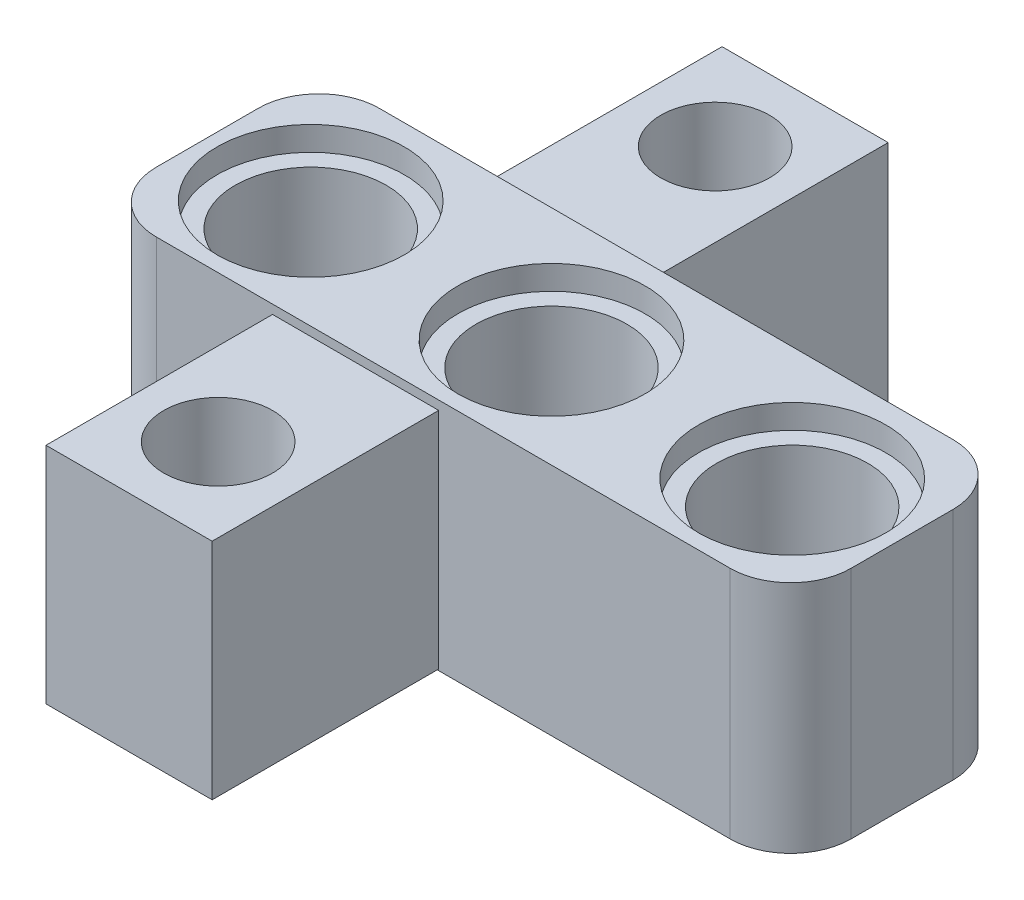
SolidWorks part; units mm, degrees
ref_plane "Front Plane" through (0, 0, 0) normal (0, 0, 1) x (1, 0, 0)
ref_plane "Top Plane" through (0, 0, 0) normal (0, 1, 0) x (1, 0, 0)
ref_plane "Right Plane" through (0, 0, 0) normal (1, 0, 0) x (0, 0, -1)
sketch "Sketch3" plane through (0, 0, 0) normal (0, 1, 0) x (1, 0, 0)
  line L1 (0, 0) -> (-23, 0)
  line L2 (0, 0) -> (0, 7.38)
  line L3 (0, 7.38) -> (-23, 7.38)
  line L4 (-23, 0) -> (-23, 7.38)
  dimension "D1" = 23
  dimension "D2" = 7.38
extrude "Boss-Extrude1" add sketch "Sketch3" along normal blind 7.76
sketch "Sketch4" plane through (0, 0, 0) normal (0, -1, 0) x (-1, 0, 0)
  line L0 (23, 0) -> (0, 0) construction
  circle A0 centre (19.5383, 3.69) radius 3.1
  circle A1 centre (11.5383, 3.69) radius 3.1
  circle A2 centre (3.5383, 3.69) radius 3.1
  dimension "D1" = 6.2
  dimension "D2" = 3.69
  dimension "D3" = 3
extrude "Cut-Extrude2" cut sketch "Sketch4" against normal blind 0.8
sketch "Sketch6" plane through (0, 0.8, 0) normal (0, -1, 0) x (-1, 0, 0)
  circle A0 centre (3.5383, 3.5915) radius 2.5
  circle A1 centre (3.5383, 3.69) radius 3.1 construction
  circle A2 centre (11.5083, 3.5915) radius 2.5
  circle A3 centre (19.4783, 3.5915) radius 2.5
  dimension "D2" = 5
  dimension "D1" = 0
  dimension "D3" = 3
sketch "Sketch7" plane through (0, 7.76, 0) normal (0, 1, 0) x (1, 0, 0)
  circle A0 centre (-19.4783, 3.5915) radius 3.1
  circle A3 centre (-11.5083, 3.5915) radius 3.1
  circle A4 centre (-3.5383, 3.5915) radius 3.1
  dimension "D1" = 6.2
  dimension "D2" = 3
extrude "Cut-Extrude3" cut sketch "Sketch7" against normal blind 0.8
extrude "Cut-Extrude4" cut sketch "Sketch6" against normal through all
fillet "Fillet3" radius 2 1 edges at (0, 3.88, 0)
fillet "Fillet4" radius 2 1 edges at (-23, 3.88, 0)
fillet "Fillet5" radius 2 1 edges at (-23, 3.88, -7.38)
fillet "Fillet6" radius 2 1 edges at (0, 3.88, -7.38)
sketch "Sketch8" plane through (0, 0, -7.38) normal (0, 0, -1) x (-1, 0, 0)
  line L0 (21, 0) -> (21, 7.76) construction
  line L1 (11.65, 0.1997) -> (17.15, 0.1997)
  line L2 (11.65, 0.1997) -> (11.65, 7.7003)
  line L3 (11.65, 7.7003) -> (17.15, 7.7003)
  line L4 (17.15, 0.1997) -> (17.15, 7.7003)
  dimension "D1" = 3.85
  dimension "D2" = 5.5
extrude "Boss-Extrude2" add sketch "Sketch8" along normal blind 7.5
sketch "Sketch9" plane through (0, 7.7003, 0) normal (0, 1, 0) x (1, 0, 0)
  line L0 (-17.15, 14.88) -> (-17.15, 7.38) construction
  circle A0 centre (-14.4, 11.9025) radius 1.8
  dimension "D2" = 3.6
  dimension "D1" = 2.75
sketch "Sketch12" plane through (0, 0, 0) normal (0, 0, 1) x (1, 0, 0)
  line L0 (-21, 7.76) -> (-21, 0) construction
  line L1 (-17.15, 7.4628) -> (-11.65, 7.4628)
  line L2 (-17.15, 7.4628) -> (-17.15, 0.0473)
  line L3 (-17.15, 0.0473) -> (-11.65, 0.0473)
  line L4 (-11.65, 7.4628) -> (-11.65, 0.0473)
  dimension "D1" = 5.5
  dimension "D3" = 3.85
extrude "Boss-Extrude4" add sketch "Sketch12" along normal blind 7.5
sketch "Sketch13" plane through (0, 7.4628, 0) normal (0, 1, 0) x (1, 0, 0)
  line L0 (-11.65, -7.5) -> (-11.65, 0) construction
  circle A0 centre (-14.4, -4.5507) radius 1.8
  dimension "D1" = 2.75
  dimension "D2" = 3.6
extrude "Cut-Extrude5" cut sketch "Sketch9" against normal blind 20.6
extrude "Cut-Extrude6" cut sketch "Sketch13" against normal blind 20.6
sketch "Sketch14" plane through (0, 0, 0) normal (0, -1, 0) x (-1, 0, 0)
  circle A0 centre (6.6383, 3.69) radius 2.3
  circle A1 centre (3.5383, 3.69) radius 3.1 construction
  dimension "D1" = 4.6
extrude "Cut-Extrude7" cut sketch "Sketch14" against normal blind 2.5
